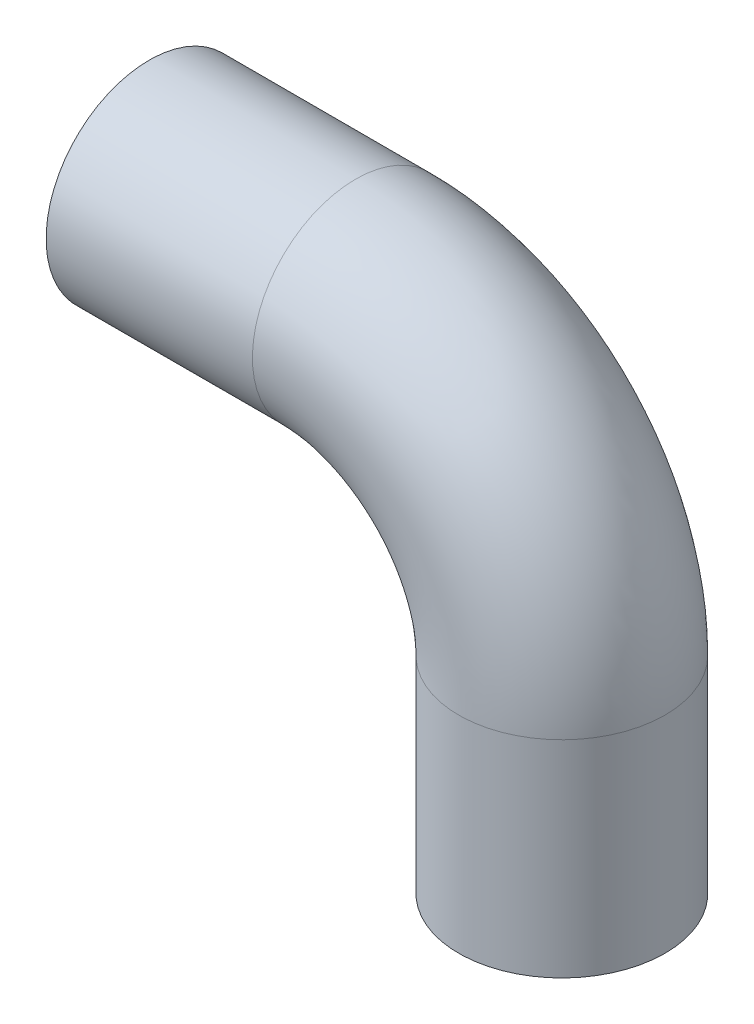
SolidWorks part; units mm, degrees
ref_plane "前视基准面" through (0, 0, 0) normal (0, 0, 1) x (1, 0, 0)
ref_plane "上视基准面" through (0, 0, 0) normal (0, 1, 0) x (1, 0, 0)
ref_plane "右视基准面" through (0, 0, 0) normal (1, 0, 0) x (0, 0, -1)
sketch "草图2" plane through (0, 0, 0) normal (0, 0, 1) x (1, 0, 0)
  line L0 (0, 0) -> (10, 0)
  line L1 (20, -10) -> (20, -20)
  arc A0 (10, 0) -> (20, -10) centre (10, -10) cw
  point P6 (20, 0)
  dimension "D3" = 10
  dimension "D1" = 20
  dimension "D2" = 20
sketch "草图48" plane through (0, 0, 0) normal (1, 0, 0) x (0, 0, -1)
  circle A0 centre (0, 0) radius 5
  dimension "D1" = 10
sweep "扫描7" add profiles "草图48" path "草图2"
